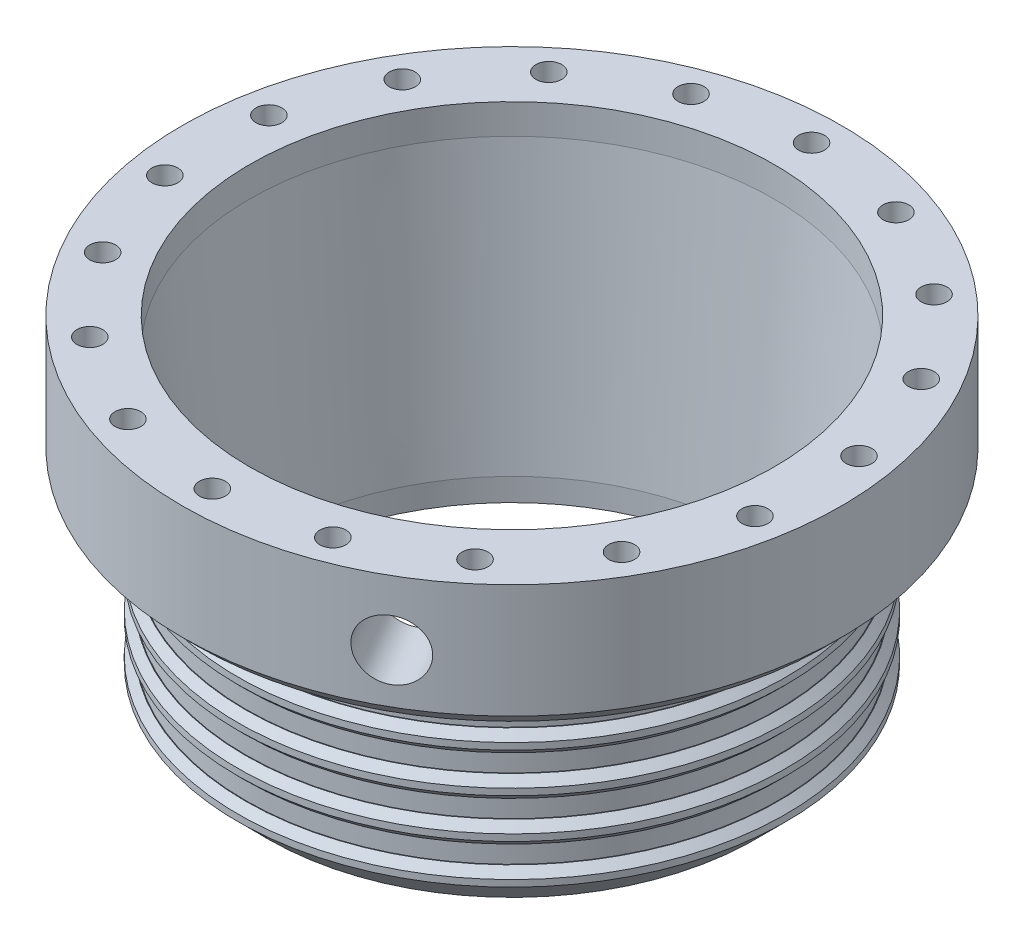
SolidWorks part; units mm, degrees
material "6061-T4 (SS)"
ref_plane "Front Plane" through (0, 0, 0) normal (0, 0, 1) x (1, 0, 0)
ref_plane "Top Plane" through (0, 0, 0) normal (0, 1, 0) x (1, 0, 0)
ref_plane "Right Plane" through (0, 0, 0) normal (1, 0, 0) x (0, 0, -1)
sketch "Sketch1" plane through (0, 0, 0) normal (0, 1, 0) x (1, 0, 0)
  circle A0 centre (0, 0) radius 55.5625
  circle A1 centre (0, 0) radius 58.1025
  dimension "D1" = 111.125
  dimension "D2" = 2.54
extrude "Boss-Extrude1" add sketch "Sketch1" along normal blind 38.1
sketch "Sketch2" plane through (0, 38.1, 0) normal (0, 1, 0) x (1, 0, 0)
  circle A0 centre (0, 0) radius 55.5625
  circle A1 centre (0, 0) radius 69.85
  circle A2 centre (0, 0) radius 55.5625 construction
  dimension "D1" = 139.7
extrude "Boss-Extrude2" add sketch "Sketch2" along normal blind 20.955
sketch "Sketch7" plane through (0, 0, 0) normal (0, 0, 1) x (1, 0, 0)
  line L0 (0, 0) -> (0, 88.9) construction
ref_plane "Plane1" through (0, 0, 0) normal (0.9659, 0, -0.2588) x (0, 1, 0)
ref_plane "Plane2" through (18.0785, 0, 67.4699) normal (0.2588, 0, 0.9659) x (0.9659, 0, -0.2588)
sketch "Sketch9" plane through (0, 0, 0) normal (0, 0, 1) x (1, 0, 0)
  line L0 (0, 0) -> (0, 88.9) construction
  line L2 (0, 0) -> (-58.1025, 0) construction
  line L3 (-58.1025, 0) -> (58.1025, 0) construction
  line L4 (-58.1025, 0) -> (-58.1025, 38.1) construction
  line L5 (-69.85, 38.1) -> (69.85, 38.1) construction
  line L6 (-58.1025, 38.1) -> (58.1025, 38.1) construction
  line L7 (-58.1025, 38.1) -> (-58.1025, 33.528)
  line L8 (-58.1025, 4.572) -> (-56.388, 4.572)
  line L9 (-58.1025, 4.572) -> (-58.1025, 8.382)
  line L10 (-58.1025, 8.382) -> (-56.388, 8.382)
  line L11 (-56.388, 4.572) -> (-56.388, 8.382)
  line L12 (-58.1025, 12.954) -> (-56.388, 12.954)
  line L13 (-58.1025, 12.954) -> (-58.1025, 16.764)
  line L14 (-58.1025, 16.764) -> (-56.388, 16.764)
  line L15 (-56.388, 12.954) -> (-56.388, 16.764)
  line L16 (-58.1025, 21.336) -> (-56.388, 21.336)
  line L17 (-58.1025, 21.336) -> (-58.1025, 25.146)
  line L18 (-58.1025, 25.146) -> (-56.388, 25.146)
  line L19 (-56.388, 21.336) -> (-56.388, 25.146)
  line L20 (-58.1025, 29.718) -> (-56.388, 29.718)
  line L21 (-58.1025, 29.718) -> (-58.1025, 33.528)
  line L22 (-58.1025, 33.528) -> (-56.388, 33.528)
  line L23 (-56.388, 29.718) -> (-56.388, 33.528)
  line L24 (-58.1025, 29.718) -> (-58.1025, 25.146)
  line L25 (-58.1025, 21.336) -> (-58.1025, 16.764)
  line L26 (-58.1025, 12.954) -> (-58.1025, 8.382)
  line L27 (-58.1025, 4.572) -> (-58.1025, 0)
  dimension "D1" = 58.1025
  dimension "D2" = 1.7145
  dimension "D3" = 3.81
revolve "Cut-Revolve1" cut sketch "Sketch9" angle 360 about L0
chamfer "Chamfer1" distance 1.5875 angle 45 1 edges at (0, 0, 58.1025)
sketch "Sketch10" plane through (0, 0, 0) normal (0, 0, 1) x (1, 0, 0)
  line L0 (0, 0) -> (0, 88.7441) construction
  line L1 (0, 0) -> (55.5625, 0) construction
  line L2 (55.5625, 0) -> (55.5625, 59.055)
  line L3 (55.5625, 59.055) -> (50.8, 0)
  line L4 (50.8, 0) -> (55.5625, 0)
  dimension "D1" = 55.5625
  dimension "D2" = 59.055
  dimension "D3" = 50.8
revolve "Revolve1" add sketch "Sketch10" angle 360 about L0
sketch "Sketch16" plane through (0, 59.055, 0) normal (0, 1, 0) x (1, 0, 0)
  circle A0 centre (0, 0) radius 69.85
  circle A1 centre (0, 0) radius 55.5625
  circle A3 centre (0, 0) radius 69.85 construction
  circle A5 centre (0, 0) radius 55.5625 construction
extrude "Boss-Extrude3" add sketch "Sketch16" along normal blind 6.35
sketch "Sketch11" plane through (0, 65.405, 0) normal (0, 1, 0) x (1, 0, 0)
  circle A0 centre (0, 0) radius 61.9633
  circle A1 centre (0, 0) radius 59.3217
  dimension "D1" = 123.9266
  dimension "D2" = 2.6416
sketch "Sketch12" plane through (0, 65.405, 0) normal (0, 1, 0) x (1, 0, 0)
  circle A0 centre (0, 0) radius 63.5 construction
  circle A1 centre (0, -63.5) radius 2.7432
  dimension "D1" = 5.4864
  dimension "D2" = 127
extrude "Cut-Extrude7" cut sketch "Sketch12" against normal blind 20.955 contours A1
pattern_circular "CirPattern2" count 18 over 360 about axis through (0, 0, 0) along (0, 1, 0) of "Cut-Extrude7"
sketch "Sketch13" plane through (0, 0, 0) normal (0, 0, 1) x (1, 0, 0)
  line L0 (0, 0) -> (50.8, 0) construction
  line L1 (0, 0) -> (0, 34.9502) construction
  line L2 (50.8, 0) -> (56.515, 0)
  line L3 (50.8, 0) -> (50.8, -5.715)
  line L4 (56.515, 0) -> (50.8, -5.715)
  dimension "D1" = 50.8
  dimension "D2" = 5.715
  dimension "D3" = 45
revolve "Revolve2" add sketch "Sketch13" angle 360 about L1
chamfer "Chamfer2" distance 1.27 angle 45 1 edges at (0, -5.715, -50.8)
sketch "Sketch14" plane through (0, 65.405, 0) normal (0, 1, 0) x (1, 0, 0)
  line L0 (0, -63.5) -> (54.9926, -31.75) construction
  line L1 (0, -38.6221) -> (0, 38.6221) construction
  line L2 (0, 0) -> (27.4963, -47.625) construction
  circle A1 centre (0, -63.5) radius 2.7432 construction
ref_plane "Plane3" through (27.4963, 0, 47.625) normal (0.5, 0, 0.866) x (0.866, 0, -0.5)
sketch "Sketch15" plane through (27.4963, 0, 47.625) normal (0.5, 0, 0.866) x (0.866, 0, -0.5)
  line L0 (0, 65.405) -> (0, 38.1) construction
  line L1 (-58.1025, 38.1) -> (58.1025, 38.1) construction
  circle A0 centre (0, 51.7525) radius 6.35
  dimension "D1" = 12.7
extrude "Cut-Extrude8" cut sketch "Sketch15" against normal up to next and the other way through all
chamfer "Chamfer3" distance 1.5875 angle 45 8 edges at (0, 33.528, -58.1025) (0, 29.718, -58.1025) (0, 21.336, -58.1025) (0, 25.146, -58.1025) (0, 12.954, -58.1025) (0, 16.764, -58.1025) (0, 8.382, -58.1025) (0, 4.572, -58.1025)
chamfer "Chamfer4" distance 3.175 angle 45 1 edges at (0, 38.1, 69.85)
